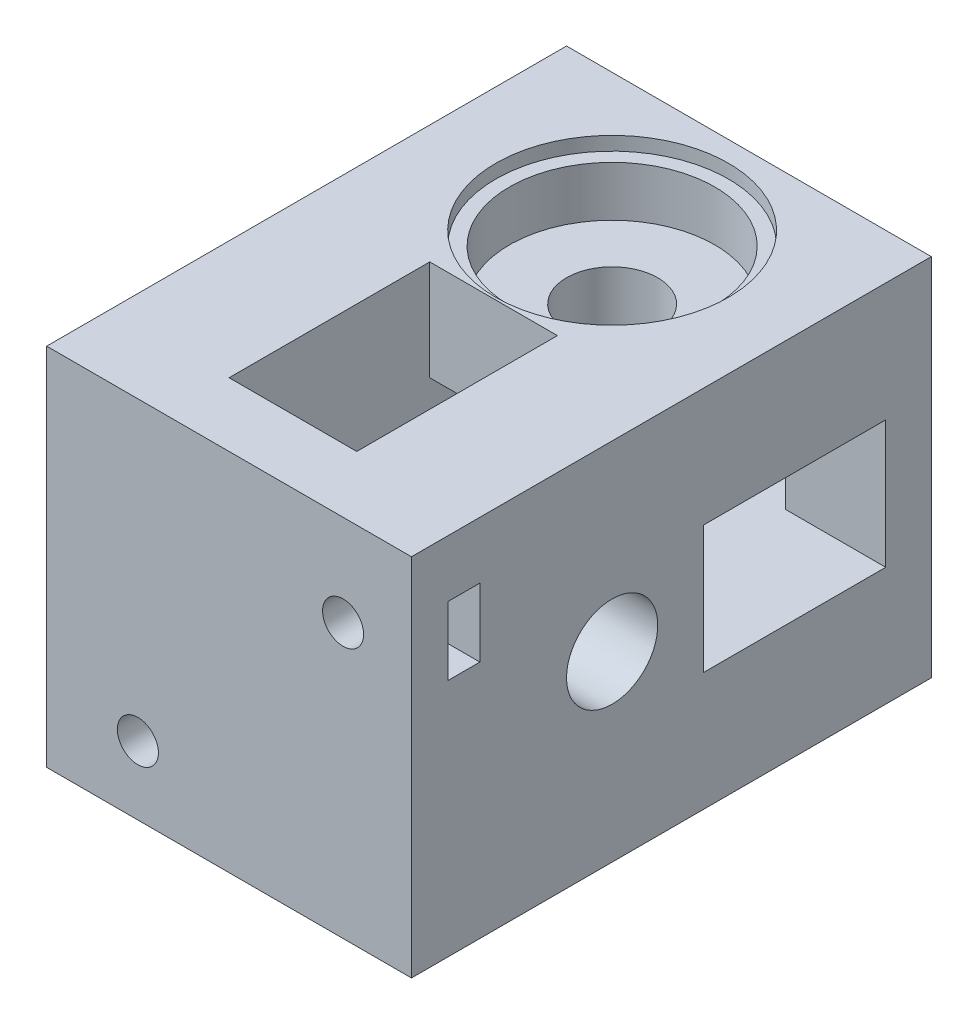
SolidWorks part; units mm, degrees
ref_plane "Plan de face" through (0, 0, 0) normal (0, 0, 1) x (1, 0, 0)
ref_plane "Plan de dessus" through (0, 0, 0) normal (0, 1, 0) x (1, 0, 0)
ref_plane "Plan de droite" through (0, 0, 0) normal (1, 0, 0) x (0, 0, -1)
sketch "Esquisse1" plane through (0, 0, 0) normal (0, 0, 1) x (1, 0, 0)
  line L1 (-40, 40) -> (0, 40)
  line L2 (-40, 40) -> (-40, 0)
  line L3 (-40, 0) -> (0, 0)
  line L4 (0, 40) -> (0, 0)
  dimension "D1" = 40
  dimension "D2" = 40
extrude "Boss.-Extru.1" add sketch "Esquisse1" along normal blind 50
sketch "Esquisse2" plane through (0, 40, 0) normal (0, 1, 0) x (1, 0, 0)
  line L0 (0, 0) -> (-40, 0) construction
  line L1 (-40, -50) -> (-40, 0) construction
  circle A0 centre (-20, -15) radius 5
  dimension "D1" = 10
  dimension "D2" = 15
  dimension "D3" = 20
extrude "Enlèv. mat.-Extru.1" cut sketch "Esquisse2" against normal through all
sketch "Esquisse3" plane through (-40, 0, 0) normal (-1, 0, 0) x (0, 0, 1)
  line L0 (50, 40) -> (50, 0) construction
  line L1 (50, 40) -> (0, 40) construction
  circle A0 centre (35, 20) radius 5
  dimension "D1" = 10
  dimension "D2" = 15
  dimension "D3" = 20
extrude "Enlèv. mat.-Extru.2" cut sketch "Esquisse3" against normal through all
sketch "Esquisse4" plane through (-40, 0, 0) normal (-1, 0, 0) x (0, 0, 1)
  line L1 (22, 27) -> (0, 27)
  line L2 (22, 27) -> (22, 13)
  line L3 (22, 13) -> (0, 13)
  line L4 (0, 27) -> (0, 13)
  line L5 (0, 40) -> (0, 0) construction
  line L6 (50, 0) -> (0, 0) construction
  line L7 (50, 40) -> (0, 40) construction
  dimension "D1" = 14
  dimension "D2" = 22
  dimension "D3" = 0
  dimension "D4" = 13
  dimension "D5" = 13
extrude "Enlèv. mat.-Extru.3" cut sketch "Esquisse4" against normal blind 29
sketch "Esquisse5" plane through (0, 0, 0) normal (0, -1, 0) x (1, 0, 0)
  line L0 (-40, 50) -> (0, 50) construction
  line L1 (-13, 25) -> (-27, 25)
  line L2 (-13, 25) -> (-13, 45)
  line L3 (-13, 45) -> (-27, 45)
  line L4 (-27, 25) -> (-27, 45)
  line L5 (-40, 50) -> (-40, 0) construction
  dimension "D1" = 20
  dimension "D2" = 5
  dimension "D3" = 14
  dimension "D4" = 13
extrude "Enlèv. mat.-Extru.4" cut sketch "Esquisse5" against normal blind 29
sketch "Esquisse6" plane through (0, 0, 0) normal (1, 0, 0) x (0, 0, -1)
  line L1 (-5, 27) -> (-25, 27)
  line L2 (0, 0) -> (0, 40) construction
  line L3 (-5, 13) -> (-25, 13)
  line L4 (-25, 27) -> (-25, 13)
  line L5 (-50, 0) -> (0, 0) construction
  line L6 (-5, 27) -> (-5, 13)
  dimension "D1" = 14
  dimension "D2" = 5
  dimension "D3" = 13
  dimension "D4" = 20
extrude "Enlèv. mat.-Extru.5" cut sketch "Esquisse6" against normal blind 24
sketch "Esquisse7" plane through (0, 40, 0) normal (0, 1, 0) x (1, 0, 0)
  line L0 (0, -50) -> (-40, -50) construction
  line L1 (-27, -50) -> (-13, -50)
  line L2 (-27, -50) -> (-27, -28)
  line L3 (-27, -28) -> (-13, -28)
  line L4 (-13, -50) -> (-13, -28)
  line L5 (-40, -50) -> (-40, 0) construction
  dimension "D1" = 14
  dimension "D2" = 22
  dimension "D3" = 13
extrude "Enlèv. mat.-Extru.6" cut sketch "Esquisse7" against normal blind 24
sketch "Esquisse10" plane through (0, 40, 0) normal (0, 1, 0) x (1, 0, 0)
  circle A0 centre (-20, -15) radius 11.25
  dimension "D1" = 22.5
extrude "Enlèv. mat.-Extru.9" cut sketch "Esquisse10" against normal blind 7
sketch "Esquisse11" plane through (0, 40, 0) normal (0, 1, 0) x (1, 0, 0)
  circle A0 centre (-20, -15) radius 12.75
  dimension "D1" = 25.5
extrude "Enlèv. mat.-Extru.10" cut sketch "Esquisse11" against normal blind 1.5
sketch "Esquisse14" plane through (-40, 0, 0) normal (-1, 0, 0) x (0, 0, 1)
  circle A0 centre (35, 20) radius 11.25
  dimension "D1" = 22.5
extrude "Enlèv. mat.-Extru.11" cut sketch "Esquisse14" against normal blind 7
sketch "Esquisse15" plane through (-40, 0, 0) normal (-1, 0, 0) x (0, 0, 1)
  circle A0 centre (35, 20) radius 12.75
  dimension "D1" = 25.5
extrude "Enlèv. mat.-Extru.12" cut sketch "Esquisse15" against normal blind 1.5
sketch "Esquisse16" plane through (0, 0, 50) normal (0, 0, 1) x (1, 0, 0)
  line L1 (0, 0) -> (-40, 0)
  line L2 (0, 0) -> (0, 40)
  line L3 (0, 40) -> (-40, 40)
  line L4 (-40, 0) -> (-40, 40)
extrude "Boss.-Extru.2" add sketch "Esquisse16" along normal blind 7
sketch "Esquisse17" plane through (0, 0, 57) normal (0, 0, 1) x (1, 0, 0)
  line L0 (-40, 40) -> (-40, 0) construction
  line L1 (0, 40) -> (-40, 40) construction
  circle A0 centre (-30, 7.5) radius 2.25
  circle A1 centre (-7.5, 30) radius 2.25
  dimension "D1" = 4.5
  dimension "D2" = 4.5
  dimension "D3" = 10
  dimension "D4" = 10
  dimension "D5" = 32.5
  dimension "D6" = 32.5
extrude "Enlèv. mat.-Extru.13" cut sketch "Esquisse17" against normal blind 15
sketch "Esquisse18" plane through (0, 0, 0) normal (0, -1, 0) x (1, 0, 0)
  line L0 (-40, 57) -> (0, 57) construction
  line L1 (-26.5, 50) -> (-33.5, 50)
  line L2 (-26.5, 50) -> (-26.5, 53)
  line L3 (-26.5, 53) -> (-33.5, 53)
  line L4 (-33.5, 50) -> (-33.5, 53)
  line L5 (-40, 57) -> (-40, 0) construction
  dimension "D1" = 7
  dimension "D2" = 3
  dimension "D3" = 4
  dimension "D4" = 6.5
extrude "Enlèv. mat.-Extru.14" cut sketch "Esquisse18" against normal blind 12
sketch "Esquisse19" plane through (0, 0, 0) normal (1, 0, 0) x (0, 0, -1)
  line L0 (-57, 0) -> (-57, 40) construction
  line L1 (-49.5, 33.75) -> (-53, 33.75)
  line L2 (-49.5, 33.75) -> (-49.5, 26.25)
  line L3 (-49.5, 26.25) -> (-53, 26.25)
  line L4 (-53, 33.75) -> (-53, 26.25)
  line L5 (-57, 40) -> (0, 40) construction
  dimension "D1" = 7.5
  dimension "D2" = 3.5
  dimension "D3" = 4
  dimension "D4" = 6.25
extrude "Enlèv. mat.-Extru.15" cut sketch "Esquisse19" against normal blind 12
